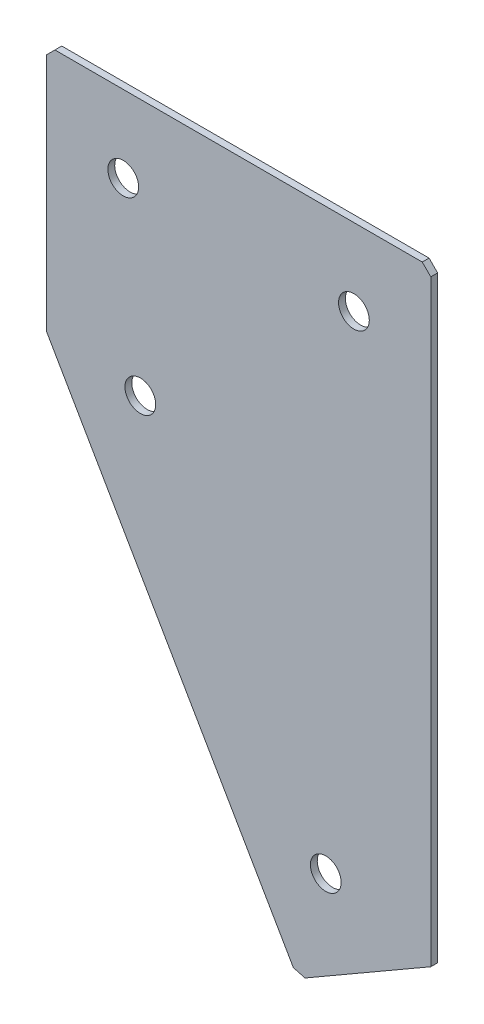
SolidWorks part; units mm, degrees
material "Простая углеродистая сталь"
ref_plane "Спереди" through (0, 0, 0) normal (0, 0, 1) x (1, 0, 0)
ref_plane "Сверху" through (0, 0, 0) normal (0, 1, 0) x (1, 0, 0)
ref_plane "Справа" through (0, 0, 0) normal (1, 0, 0) x (0, 0, -1)
sketch "Эскиз3" plane through (0, 0, 0) normal (0, 0, -1) x (1, 0, 0)
  line L0 (0, 0) -> (112.5, 0)
  line L1 (112.5, 0) -> (112.5, 177.3557)
  line L2 (0, 0) -> (0, 72.5)
  line L3 (0, 72.5) -> (73.5289, 199.8557)
  line L4 (73.5289, 199.8557) -> (112.5, 177.3557)
  dimension "D1" = 112.5
  dimension "D2" = 72.5
  dimension "D3" = 45
  dimension "D4" = 60
  dimension "D5" = 177.3557
extrude "Бобышка-Вытянуть1" add sketch "Эскиз3" along normal blind 2
hole_wizard "Отверстие с зазором M81" positions "Эскиз4" profile "Эскиз5" hole size "M8" standard "DIN" end condition through all
sketch "Эскиз4" plane through (0, 0, -2) normal (0, 0, -1) x (1, 0, 0)
  line L0 (27.5, 75.1314) -> (81.7644, 169.1201) construction
  line L2 (73.5289, 199.8557) -> (0, 72.5) construction
  line L3 (22.5, 22.5) -> (90, 22.5) construction
  line L5 (0, 0) -> (112.5, 0) construction
  line L6 (0, 72.5) -> (0, 0) construction
  line L7 (112.5, 0) -> (112.5, 177.3557) construction
  line L8 (112.5, 177.3557) -> (73.5289, 199.8557) construction
  line L9 (27.5, 75.1314) -> (0, 27.5) construction
  point P0 (22.5, 22.5)
  point P2 (90, 22.5)
  point P4 (27.5, 75.1314)
  point P6 (81.7644, 169.1201)
  dimension "D1" = 22.5
  dimension "D2" = 22.5
  dimension "D3" = 22.5
  dimension "D4" = 22.5
  dimension "D5" = 22.5
  dimension "D6" = 55
  dimension "D7" = 108.5289
  dimension "D8" = 67.5
sketch "Эскиз5" plane through (22.5, -22.5, -2) normal (1, 0, 0) x (0, 1, 0)
  line L0 (0, 0) -> (0, 2)
  line L1 (0, 2) -> (4.5, 2)
  line L2 (4.5, 2) -> (4.5, 0)
  line L5 (4.5, 0) -> (0, 0)
  line L11 (0, -6.35) -> (0, 107.95) construction
  dimension "Диаметр сквозного отверстия" = 9
  dimension "Глубина сквозного отверстия" = 2
chamfer "Фаска1" distance 2.5 distance2 2.5 3 edges at (73.5289, -199.8557, -1) (112.5, 0, -1) (0, 0, -1)
